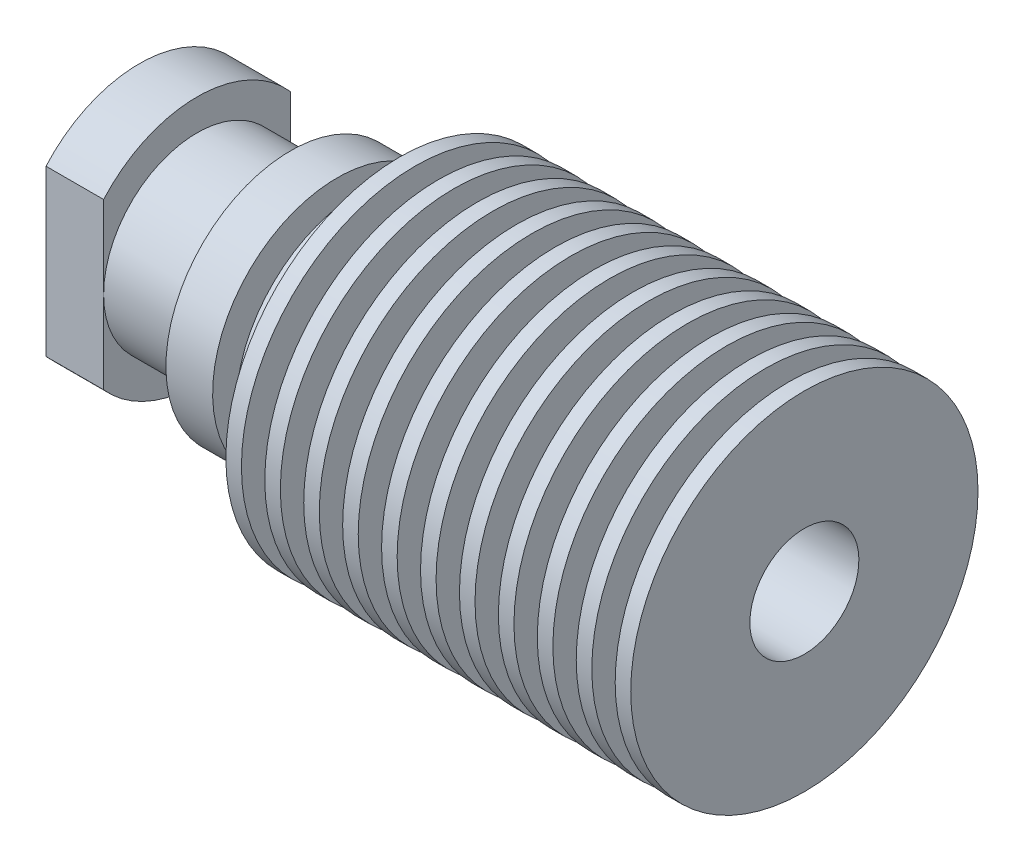
SolidWorks part; units mm, degrees
material "1060 Alloy"
ref_plane "Front Plane" through (0, 0, 0) normal (0, 0, 1) x (1, 0, 0)
ref_plane "Top Plane" through (0, 0, 0) normal (0, 1, 0) x (1, 0, 0)
ref_plane "Right Plane" through (0, 0, 0) normal (1, 0, 0) x (0, 0, -1)
sketch "Sketch1" plane through (0, 0, 0) normal (0, 0, 1) x (1, 0, 0)
  line L30 (42.7, -3.5) -> (42.7, -11.15)
  line L61 (0, 0) -> (42.7, 0) construction
  line L62 (25.2, -11.15) -> (24.2, -11.15)
  line L63 (25.2, -5.2139) -> (25.2, -11.15)
  line L64 (26.7, -5.2139) -> (25.2, -5.2139)
  line L65 (26.7, -11.15) -> (26.7, -5.2139)
  line L66 (27.7, -11.15) -> (26.7, -11.15)
  line L67 (27.7, -5.3449) -> (27.7, -11.15)
  line L68 (29.2, -5.3449) -> (27.7, -5.3449)
  line L69 (29.2, -11.15) -> (29.2, -5.3449)
  line L70 (30.2, -11.15) -> (29.2, -11.15)
  line L71 (30.2, -5.4759) -> (30.2, -11.15)
  line L72 (31.7, -5.4759) -> (30.2, -5.4759)
  line L73 (31.7, -11.15) -> (31.7, -5.4759)
  line L74 (32.7, -11.15) -> (31.7, -11.15)
  line L75 (32.7, -5.6069) -> (32.7, -11.15)
  line L76 (34.2, -5.6069) -> (32.7, -5.6069)
  line L77 (34.2, -11.15) -> (34.2, -5.6069)
  line L78 (35.2, -11.15) -> (34.2, -11.15)
  line L79 (35.2, -5.738) -> (35.2, -11.15)
  line L80 (36.7, -5.738) -> (35.2, -5.738)
  line L81 (36.7, -11.15) -> (36.7, -5.738)
  line L82 (37.7, -11.15) -> (36.7, -11.15)
  line L83 (37.7, -5.869) -> (37.7, -11.15)
  line L84 (39.2, -5.869) -> (37.7, -5.869)
  line L85 (39.2, -11.15) -> (39.2, -5.869)
  line L86 (40.2, -11.15) -> (39.2, -11.15)
  line L87 (40.2, -6) -> (40.2, -11.15)
  line L88 (41.7, -6) -> (40.2, -6)
  line L89 (41.7, -11.15) -> (41.7, -6)
  line L90 (42.7, -11.15) -> (41.7, -11.15)
  line L91 (29.4, -3.5) -> (42.7, -3.5)
  line L92 (28, -2.1) -> (29.4, -3.5)
  line L93 (8, -2.1) -> (28, -2.1)
  line L94 (6.1, -4) -> (8, -2.1)
  line L95 (0, -4) -> (6.1, -4)
  line L96 (0, -8) -> (0, -4)
  line L97 (3.7, -8) -> (0, -8)
  line L98 (3.7, -6) -> (3.7, -8)
  line L99 (9.7, -6) -> (3.7, -6)
  line L100 (9.7, -8) -> (9.7, -6)
  line L101 (12.7, -8) -> (9.7, -8)
  line L102 (12.7, -4.6898) -> (12.7, -8)
  line L103 (14.2, -4.6898) -> (12.7, -4.6898)
  line L104 (14.2, -8) -> (14.2, -4.6898)
  line L105 (15.2, -8) -> (14.2, -8)
  line L106 (15.2, -4.6898) -> (15.2, -8)
  line L107 (16.7, -4.6898) -> (15.2, -4.6898)
  line L108 (16.7, -11.15) -> (16.7, -4.6898)
  line L109 (17.7, -11.15) -> (16.7, -11.15)
  line L110 (17.7, -4.8208) -> (17.7, -11.15)
  line L111 (19.2, -4.8208) -> (17.7, -4.8208)
  line L112 (19.2, -11.15) -> (19.2, -4.8208)
  line L113 (20.2, -11.15) -> (19.2, -11.15)
  line L114 (20.2, -4.9518) -> (20.2, -11.15)
  line L115 (21.7, -4.9518) -> (20.2, -4.9518)
  line L116 (21.7, -11.15) -> (21.7, -4.9518)
  line L117 (22.7, -11.15) -> (21.7, -11.15)
  line L118 (22.7, -5.0829) -> (22.7, -11.15)
  line L119 (24.2, -5.0829) -> (22.7, -5.0829)
  line L120 (24.2, -11.15) -> (24.2, -5.0829)
revolve "Revolve1" add sketch "Sketch1" angle 360 about L61
sketch "Sketch2" plane through (0, 0, 0) normal (-1, 0, 0) x (0, 0, 1)
  line L0 (6, 5.2915) -> (6, -5.2915)
  line L1 (-6, 5.2915) -> (-6, -5.2915)
  arc A1 (-6, 5.2915) -> (-6, -5.2915) centre (0, 0) ccw
  arc A2 (6, -5.2915) -> (6, 5.2915) centre (0, 0) ccw
  dimension "D2" = 16
  dimension "D1" = 6
  dimension "D3" = 6
extrude "Cut-Extrude1" cut sketch "Sketch2" against normal up to next
